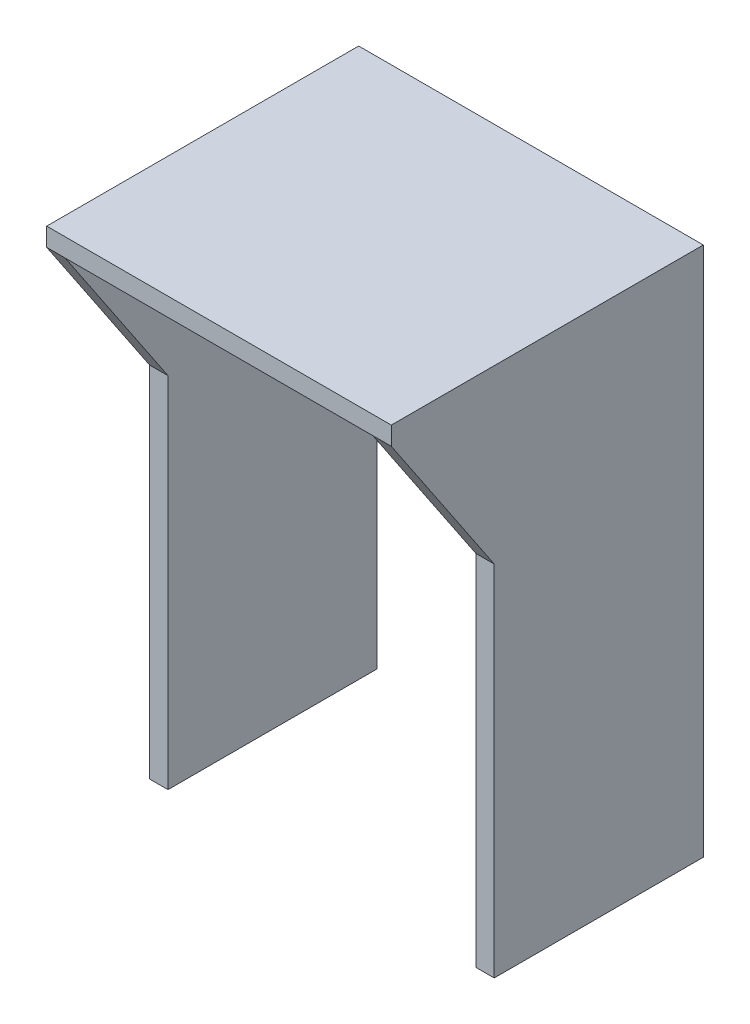
SolidWorks part; units mm, degrees
ref_plane "Front Plane" through (0, 0, 0) normal (0, 0, 1) x (1, 0, 0)
ref_plane "Top Plane" through (0, 0, 0) normal (0, 1, 0) x (1, 0, 0)
ref_plane "Right Plane" through (0, 0, 0) normal (1, 0, 0) x (0, 0, -1)
sketch "Sketch1" plane through (0, 0, 0) normal (0, 0, 1) x (1, 0, 0)
  line L0 (0, 0) -> (0, 63.4)
  line L1 (0, 63.4) -> (41.2, 63.4)
  line L2 (41.2, 63.4) -> (41.2, 0)
  line L3 (41.2, 0) -> (39, 0)
  line L4 (39, 0) -> (39, 61.2)
  line L5 (39, 61.2) -> (2.2, 61.2)
  line L6 (2.2, 61.2) -> (2.2, 0)
  line L7 (2.2, 0) -> (0, 0)
  dimension "D1" = 63.4
  dimension "D2" = 41.2
  dimension "D3" = 2.2
  dimension "D4" = 2.2
  dimension "D5" = 2.2
sketch "Sketch2" plane through (0, 0, 0) normal (1, 0, 0) x (0, 0, -1)
  line L0 (0, 0) -> (-25, 0)
  line L1 (-25, 0) -> (-25, 42.8671)
  line L2 (-25, 42.8671) -> (-37.3, 61.2)
  line L3 (-37.3, 61.2) -> (-37.3, 63.4)
  line L4 (-37.3, 63.4) -> (0, 63.4)
  line L5 (0, 63.4) -> (0, 0) construction
  line L6 (0, 0) -> (0, 63.4) construction
  line L7 (0, 63.4) -> (0, 0)
  dimension "D1" = 37.3
  dimension "D2" = 25
  dimension "D3" = 2.2
extrude "Boss-Extrude1" add sketch "Sketch2" along normal up to vertex (41.2 mm away) contours L4 L7 L0 L1 L2 L3 up to point (41.2, 63.4, 0)
sketch "Sketch4" plane through (0, 0, 0) normal (0, 0, 1) x (1, 0, 0)
  line L0 (2.2, 61.2) -> (2.2, 0)
  line L1 (2.2, 0) -> (39, 0)
  line L2 (39, 0) -> (39, 61.2)
  line L3 (39, 61.2) -> (2.2, 61.2)
extrude "Cut-Extrude1" cut sketch "Sketch4" along normal blind 10000
